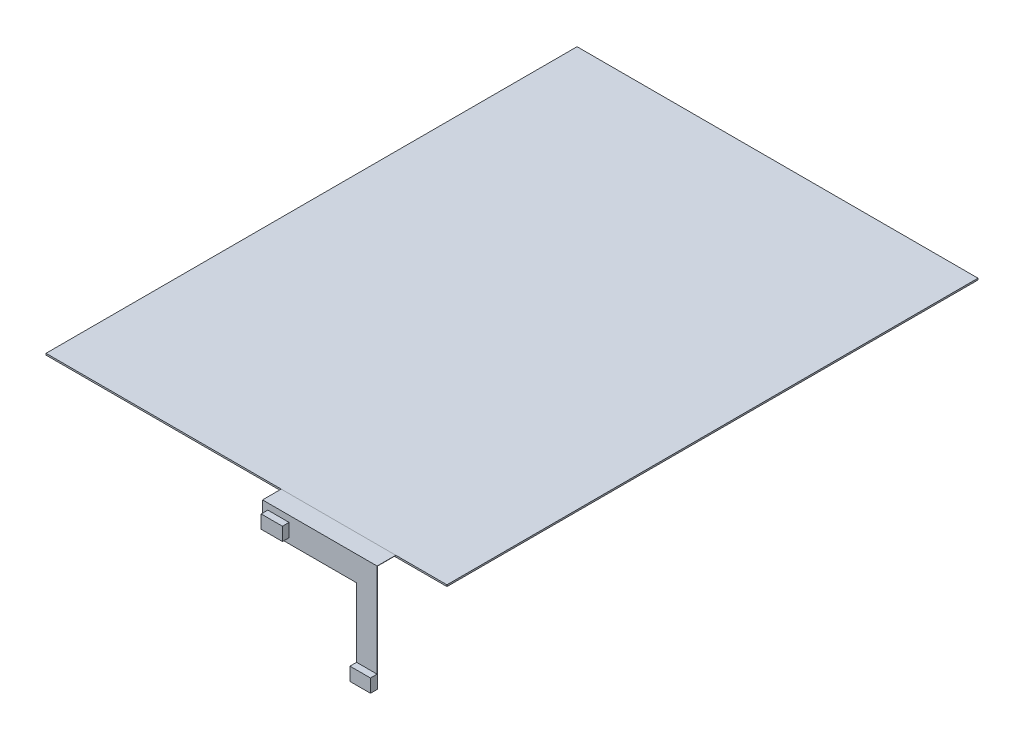
SolidWorks part; units mm, degrees
material "PA Tipo 6"
ref_plane "Alzado" through (0, 0, 0) normal (0, 0, 1) x (1, 0, 0)
ref_plane "Planta" through (0, 0, 0) normal (0, 1, 0) x (1, 0, 0)
ref_plane "Vista lateral" through (0, 0, 0) normal (1, 0, 0) x (0, 0, -1)
sketch "Croquis1" plane through (0, 0, 0) normal (0, 1, 0) x (1, 0, 0)
  line L1 (75.5, -100) -> (-75.5, -100)
  line L2 (75.5, -100) -> (75.5, 100)
  line L3 (75.5, 100) -> (-75.5, 100)
  line L4 (-75.5, -100) -> (-75.5, 100)
  line L5 (75.5, -100) -> (-75.5, 100) construction
  line L6 (75.5, 100) -> (-75.5, -100) construction
  point P0 (0, 0)
  dimension "D1" = 151
  dimension "D2" = 200
extrude "Saliente-Extruir1" add sketch "Croquis1" along normal blind 0.6
sketch "Croquis4" plane through (0, 0.6, 0) normal (0, 1, 0) x (1, 0, 0)
  line L0 (56.2334, -100) -> (56.2334, -107.0383)
  line L1 (-75.5, -100) -> (75.5, -100) construction
  line L2 (56.2334, -107.0383) -> (13.084, -107.0383)
  line L3 (13.084, -107.0383) -> (13.084, -100)
  line L4 (13.084, -100) -> (56.2334, -100)
extrude "Saliente-Extruir2" add sketch "Croquis4" against normal blind 0.1 separate body
sketch "Croquis5" plane through (0, 0, 107.0383) normal (0, 0, 1) x (1, 0, 0)
  line L0 (56.2334, 0.5) -> (56.2334, -39.6648)
  line L1 (56.2334, -39.6648) -> (48.5073, -39.6648)
  line L2 (48.5073, -39.6648) -> (48.5073, -8.7402)
  line L3 (48.5073, -8.7402) -> (13.084, -8.7402)
  line L4 (13.084, -8.7402) -> (13.084, 0.5)
  line L5 (13.084, 0.5) -> (56.2334, 0.5)
extrude "Saliente-Extruir3" add sketch "Croquis5" against normal blind 0.1
sketch "Croquis7" plane through (0, 0, 107.0383) normal (0, 0, 1) x (1, 0, 0)
  line L0 (48.5073, -8.7402) -> (48.5073, -39.6648) construction
  line L1 (48.5073, -39.6648) -> (56.2334, -39.6648)
  line L2 (48.5073, -39.6648) -> (48.5073, -34.6648)
  line L3 (48.5073, -34.6648) -> (56.2334, -34.6648)
  line L4 (56.2334, -39.6648) -> (56.2334, -34.6648)
  line L5 (56.2334, -39.6648) -> (56.2334, 0.6) construction
  line L6 (48.5073, -39.6648) -> (56.2334, -39.6648) construction
  line L7 (13.084, -8.7402) -> (13.084, 0.6) construction
  line L8 (15.084, -1.7402) -> (23.084, -1.7402)
  line L9 (15.084, -1.7402) -> (15.084, -6.7402)
  line L10 (15.084, -6.7402) -> (23.084, -6.7402)
  line L11 (23.084, -1.7402) -> (23.084, -6.7402)
  line L12 (13.084, -8.7402) -> (48.5073, -8.7402) construction
  dimension "D1" = 5
  dimension "D2" = 5
  dimension "D3" = 8
  dimension "D4" = 2
  dimension "D5" = 2
extrude "Saliente-Extruir5" add sketch "Croquis7" along normal blind 2.5
